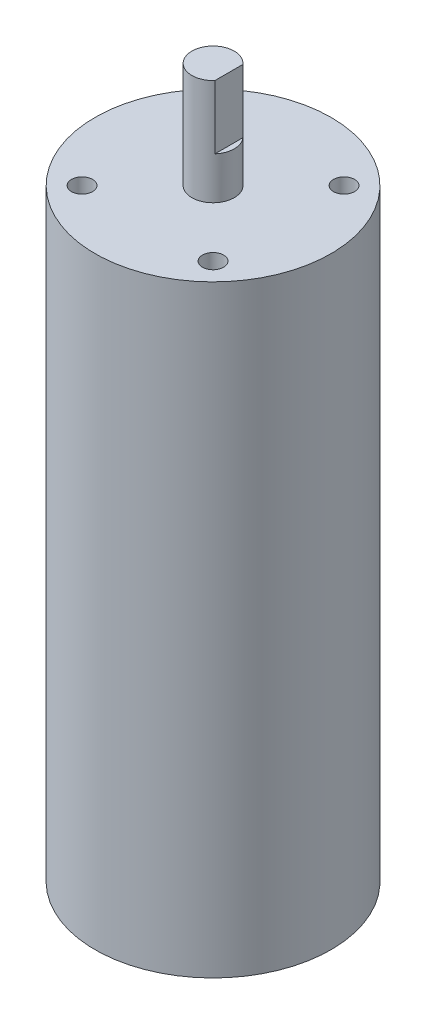
SolidWorks part; units mm, degrees
ref_plane "Front Plane" through (0, 0, 0) normal (0, 0, 1) x (1, 0, 0)
ref_plane "Top Plane" through (0, 0, 0) normal (0, 1, 0) x (1, 0, 0)
ref_plane "Right Plane" through (0, 0, 0) normal (1, 0, 0) x (0, 0, -1)
sketch "Sketch2" plane through (0, 0, 0) normal (0, 0, 1) x (1, 0, 0)
  line L0 (0, 0) -> (0, 90.1897) construction
  line L1 (0, 0) -> (22.3, 0)
  line L2 (22.3, 0) -> (22.3, 113.9)
  line L3 (22.3, 113.9) -> (4, 113.9)
  line L4 (4, 113.9) -> (4, 133.9)
  line L5 (4, 133.9) -> (0, 133.9)
  line L12 (0, 133.9) -> (0, 0)
  dimension "D1" = 44.6
  dimension "D2" = 20
  dimension "D3" = 4
  dimension "D4" = 113.9
revolve "Revolve1" add sketch "Sketch2" angle 360 about L0
sketch "Sketch3" plane through (0, 0, 0) normal (0, 0, 1) x (1, 0, 0)
  line L0 (4, 133.9) -> (-4, 133.9) construction
  line L2 (4, 133.9) -> (3, 133.9)
  line L3 (4, 133.9) -> (4, 121.9)
  line L4 (4, 121.9) -> (3, 121.9)
  line L5 (3, 133.9) -> (3, 121.9)
  dimension "D1" = 1
  dimension "D2" = 12
extrude "Cut-Extrude1" cut sketch "Sketch3" against normal through all and the other way through all
sketch "Sketch4" plane through (0, 113.9, 0) normal (0, 1, 0) x (1, 0, 0)
  line L0 (-12.3744, -12.3744) -> (12.3744, 12.3744) construction
  line L1 (12.3744, -12.3744) -> (-12.3744, 12.3744) construction
  line L2 (0, 0) -> (0, 22.3) construction
  circle A0 centre (0, 0) radius 17.5 construction
  circle A1 centre (0, 0) radius 22.3 construction
  circle A2 centre (-12.3744, 12.3744) radius 2
  circle A3 centre (12.3744, 12.3744) radius 2
  circle A4 centre (12.3744, -12.3744) radius 2
  circle A5 centre (-12.3744, -12.3744) radius 2
  dimension "D1" = 35
  dimension "D3" = 4
  dimension "D2" = 45
extrude "Cut-Extrude2" cut sketch "Sketch4" against normal blind 10
